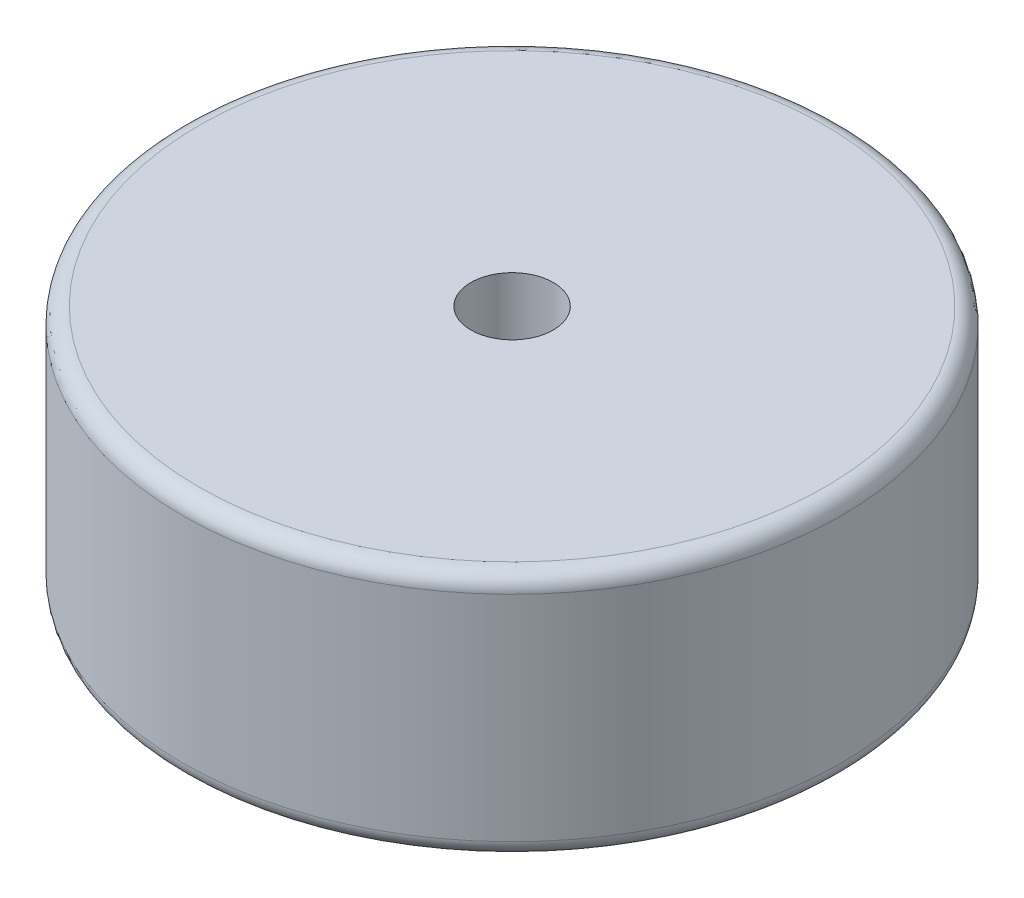
SolidWorks part; units mm, degrees
material "NEOPRENE"
ref_plane "Front Plane" through (0, 0, 0) normal (0, 0, 1) x (1, 0, 0)
ref_plane "Top Plane" through (0, 0, 0) normal (0, 1, 0) x (1, 0, 0)
ref_plane "Right Plane" through (0, 0, 0) normal (1, 0, 0) x (0, 0, -1)
sketch "Sketch1" plane through (0, 0, 0) normal (0, 1, 0) x (1, 0, 0)
  circle A0 centre (0, 0) radius 2
  circle A1 centre (0, 0) radius 0.25
  dimension "D1" = 4
  dimension "D2" = 0.5
extrude "Boss-Extrude1" add sketch "Sketch1" along normal blind 1.5
fillet "Fillet1" radius 0.1 2 edges at (0, 0, 2) (0, 1.5, 2)
